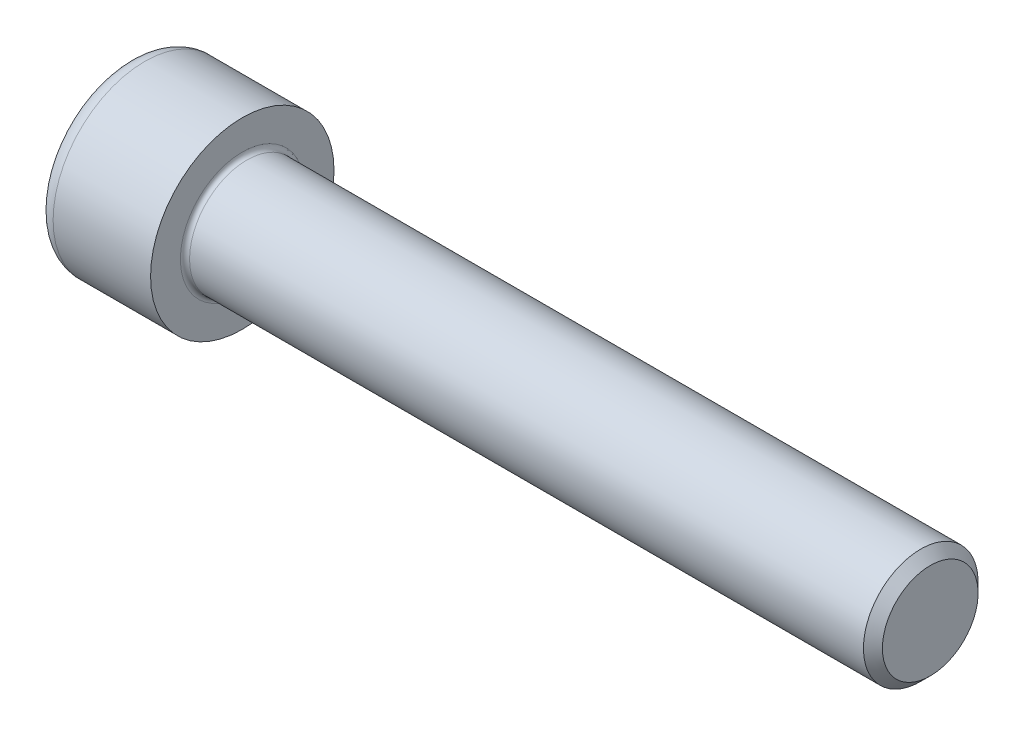
SolidWorks part; units mm, degrees
revolve "Base-Revolve" add sketch "BodySke"
sketch "BodySke" plane through (0, 0, 0) normal (0, 0, 1) x (1, 0, 0)
  line L0 (0, 0) -> (0, 8)
  line L1 (0, 8) -> (10, 8)
  line L2 (10, 8) -> (10, 5)
  line L3 (10, 5) -> (69.172, 5)
  line L4 (70, 4.172) -> (70, 0)
  line L5 (70, 0) -> (0, 0)
  line L6 (-31.75, 0) -> (127, 0) construction
  line L8 (70, 4.172) -> (69.172, 5)
  line L10 (70, -4.172) -> (69.172, -5) construction
  line L11 (11.5, 9.525) -> (11.5, 3.175) construction
  line L12 (38, 9.525) -> (38, 3.175) construction
  line L13 (10, 9.525) -> (10, 3.175) construction
  dimension "Head_ht" = 10
  dimension "Length" = 60
  dimension "Body_ch_ang" = 45
  dimension "Diameter" = 10
  dimension "Minor_dia" = 8.344
  dimension "Advance" = 1.5
  dimension "Thread_nom" = 32
  dimension "Thread_length" = 60
  dimension "Head_dia" = 16
cosmetic thread "ThreadCosmetic" [suppressed]
fillet "Fillet1" radius 0.4 1 edges at (10, 0, 5)
fillet "Fillet2" radius 1.5 1 edges at (0, 0, 8)
ref_plane "Plane1" through (0, 0, 0) normal (0, 0, 1) x (1, 0, 0)
ref_plane "Plane2" through (0, 0, 0) normal (0, 1, 0) x (1, 0, 0)
ref_plane "Plane3" through (0, 0, 0) normal (1, 0, 0) x (0, 0, -1)
sketch "Sketch2" plane through (0, 0, 0) normal (0, 0, 1) x (1, 0, 0)
  line L0 (0, 4.0575) -> (5, 4.0575)
  line L1 (5, 4.0575) -> (7.3426, 0)
  line L2 (-31.75, 0) -> (127, 0) construction
  line L3 (7.3426, 0) -> (0, 0)
  line L4 (0, 0) -> (0, 4.0575)
  line L6 (0, 0) -> (47.625, 0) construction
  dimension "D1" = 4.0575
  dimension "D2" = 60
  dimension "Depth" = 5
revolve "Hex-PreBroach" cut sketch "Sketch2" angle 360 about L6
sketch "Sketch3" plane through (0, 0, 0) normal (-1, 0, 0) x (0, 0.5, 0.866)
  line L0 (2.3426, 4.0575) -> (-2.3426, 4.0575)
  line L1 (-2.3426, 4.0575) -> (-4.6852, 0)
  line L2 (2.3426, 4.0575) -> (4.6852, 0)
  line L3 (2.3426, -4.0575) -> (4.6852, 0)
  line L4 (2.3426, -4.0575) -> (-2.3426, -4.0575)
  line L5 (-2.3426, -4.0575) -> (-4.6852, 0)
  dimension "D1" = 4.0575
  dimension "D2" = 4.0575
  dimension "Hex_size" = 8.115
extrude "Hex" cut sketch "Sketch3" against normal blind 5
sketch "ThdSchSke" plane through (0, 0, 0) normal (0, 0, 1) x (1, 0, 0)
  line L0 (38, -4.172) -> (37.4202, -5)
  line L1 (38, -4.172) -> (38.5798, -5)
  line L2 (38.5798, -5) -> (38.5798, -6.25)
  line L3 (-3.175, 0) -> (5.1513, 0) construction
  line L4 (0, 6.5) -> (0, -6.5) construction
  line L5 (38.5798, -6.25) -> (37.4202, -6.25)
  line L6 (37.4202, -6.25) -> (37.4202, -5)
  dimension "Thread_minor" = 8.344
  dimension "Diameter" = 10
  dimension "Start" = 38
revolve "ThreadSchematic" [suppressed] cut sketch "ThdSchSke" angle 360 about L3
pattern_linear "ThdSchPat" [suppressed]
equation "\"D2@Sketch3\" = \"Hex_size@Sketch3\" / 2"
equation "\"D1@Sketch3\" = \"Hex_size@Sketch3\" / 2"
equation "\"D1@Sketch2\" = \"Hex_size@Sketch3\" / 2"
equation "\"Thread_minor@ThreadCosmetic\"  =  \"Minor_dia@BodySke\""
equation "\"Depth@Sketch2\" =  \"Key_eng@Hex\""
equation "\"Thread_length@ThreadCosmetic\" = ((sgn( (\"Length@BodySke\" - \"Advance@BodySke\" * 3.0) - \"Thread_nom@BodySke\" )-1)*( (\"Length@BodySke\" - \"Advance@BodySke\" * 3.0) - \"Thread_nom@BodySke\" ))/-2+ \"Thread_nom@BodySke\""
equation "\"Thread_minor@ThdSchSke\" = \"Minor_dia@BodySke\""
equation "\"Diameter@ThdSchSke\" = \"Diameter@BodySke\""
equation "\"Overcut@ThdSchSke\" = \"Diameter@BodySke\" * 1.25"
equation "\"Start@ThdSchSke\" = \"Head_ht@BodySke\" + \"Length@BodySke\" - \"Thread_length@ThreadCosmetic\"  '---Non-countersunk---"
equation "\"Num_threads@ThdSchPat\" = int( \"Thread_length@ThreadCosmetic\" / \"Advance@BodySke\" + 0.999 )  + 1"
equation "\"Advance@ThdSchPat\" = \"Thread_length@ThreadCosmetic\" /  (\"Num_threads@ThdSchPat\" - 1) 'relax it"
equation "\"Num_threads@ThdSchPat\" = \"Num_threads@ThdSchPat\" - sgn( \"Num_threads@ThdSchPat\" - 1) '---chamfered tips only---"
